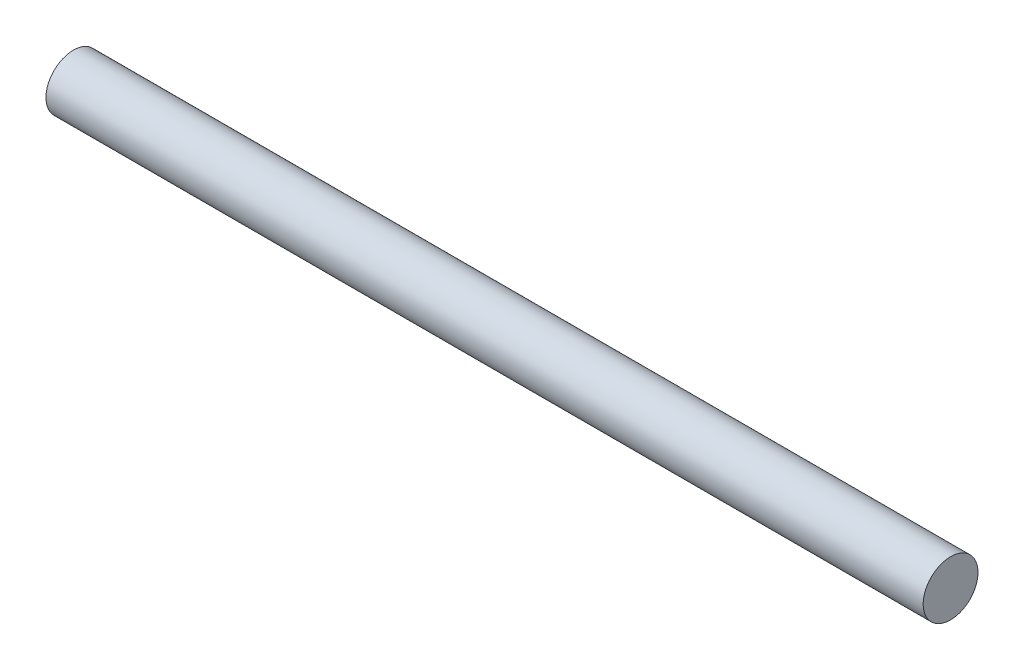
SolidWorks part; units mm, degrees
ref_plane "Front Plane" through (0, 0, 0) normal (0, 0, 1) x (1, 0, 0)
ref_plane "Top Plane" through (0, 0, 0) normal (0, 1, 0) x (1, 0, 0)
ref_plane "Right Plane" through (0, 0, 0) normal (1, 0, 0) x (0, 0, -1)
sketch "Sketch1" plane through (0, 0, 0) normal (1, 0, 0) x (0, 0, -1)
  circle A1 centre (0, 0) radius 2.5
extrude "Boss-Extrude1" add sketch "Sketch1" along normal blind 80
